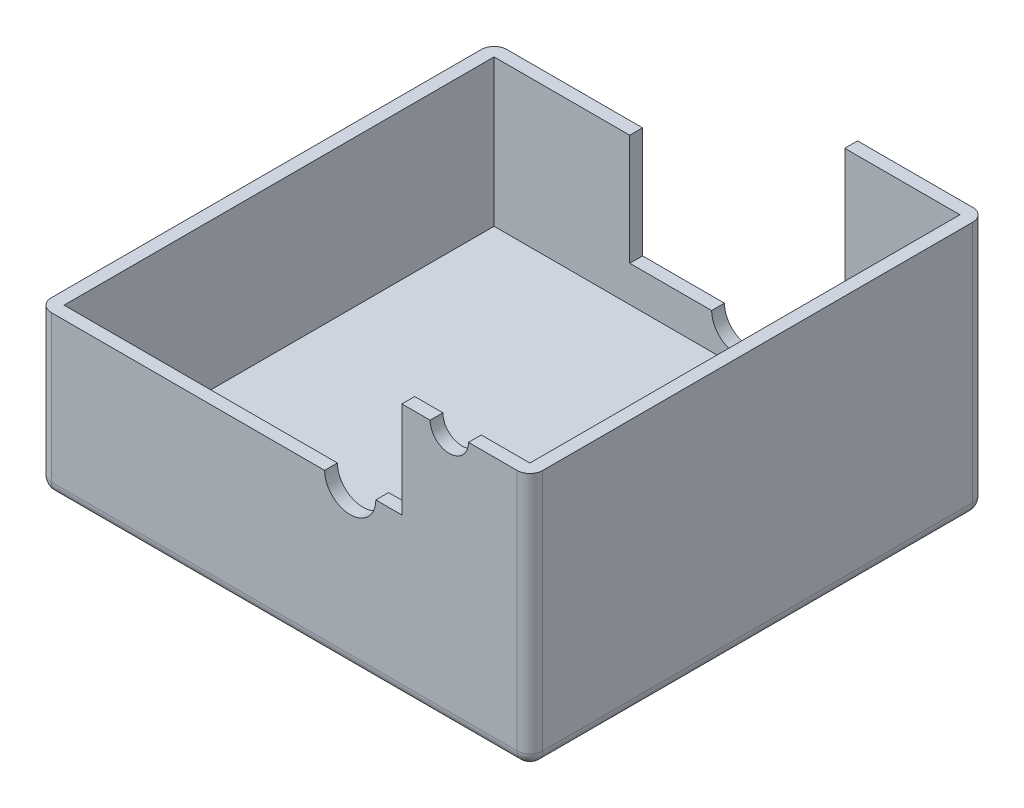
SolidWorks part; units mm, degrees
ref_plane "Front" through (0, 0, 0) normal (0, 0, 1) x (1, 0, 0)
ref_plane "Top" through (0, 0, 0) normal (0, 1, 0) x (1, 0, 0)
ref_plane "Right" through (0, 0, 0) normal (1, 0, 0) x (0, 0, -1)
sketch "Sketch1" plane through (0, 0, 0) normal (0, 1, 0) x (1, 0, 0)
  line L1 (0, 0) -> (96, 0)
  line L2 (0, 0) -> (0, -89)
  line L3 (0, -89) -> (96, -89)
  line L4 (96, 0) -> (96, -89)
  dimension "D1" = 96
  dimension "D2" = 89
extrude "Boss-Extrude1" add sketch "Sketch1" along normal blind 72.5
sketch "Sketch3" plane through (0, 72.5, 0) normal (0, 1, 0) x (1, 0, 0)
  line L8 (2.5, -2.5) -> (2.5, -86.5)
  line L9 (2.5, -86.5) -> (93.5, -86.5)
  line L10 (93.5, -86.5) -> (93.5, -2.5)
  line L11 (93.5, -2.5) -> (2.5, -2.5)
  line L12 (2.5, -2.5) -> (2.5, -86.5)
  line L13 (2.5, -86.5) -> (93.5, -86.5)
  line L14 (93.5, -86.5) -> (93.5, -2.5)
  line L15 (93.5, -2.5) -> (2.5, -2.5)
  dimension "D1" = 2.5
extrude "Cut-Extrude1" cut sketch "Sketch3" against normal blind 70 contours L12 L13 L14 L15
sketch "Sketch5" plane through (0, 0, 89) normal (0, 0, 1) x (1, 0, 0)
  line L0 (0, 0) -> (96, 0) construction
  line L2 (96, 72.5) -> (96, 0) construction
  line L3 (0, 72.5) -> (96, 72.5) construction
  line L4 (0, 72.5) -> (0, 0) construction
  line L5 (0, 31.16) -> (0, 72.5)
  line L6 (0, 72.5) -> (96, 72.5)
  line L7 (96, 72.5) -> (96, 49.95)
  line L8 (96, 49.95) -> (80.25, 49.95)
  line L9 (80.25, 49.95) -> (71, 49.95)
  line L10 (71, 49.95) -> (71, 31.16)
  line L11 (71, 31.16) -> (0, 31.16)
  dimension "D1" = 31.16
  dimension "D2" = 15.75
  dimension "D5" = 22.55
  dimension "D7" = 25
extrude "Cut-Extrude5" cut sketch "Sketch5" against normal through all
sketch "Sketch7" plane through (0, 0, 89) normal (0, 0, 1) x (1, 0, 0)
  line L0 (71, 49.95) -> (96, 49.95) construction
  line L1 (0, 31.16) -> (71, 31.16) construction
  line L2 (96, 49.95) -> (96, 0) construction
  circle A0 centre (80.25, 49.95) radius 3.75
  circle A1 centre (60.9, 31.16) radius 5
  dimension "D1" = 10
  dimension "D2" = 7.5
  dimension "D3" = 15.75
  dimension "D4" = 35.1
extrude "Cut-Extrude6" cut sketch "Sketch7" against normal blind 2.5
sketch "Sketch8" plane through (0, 0, 0) normal (0, 0, -1) x (-1, 0, 0)
  line L2 (-71, 31.16) -> (-71, 9.5)
  line L3 (-71, 9.5) -> (-29, 9.5)
  line L4 (-29, 9.5) -> (-29, 31.16)
  line L5 (0, 31.16) -> (-71, 31.16) construction
  line L6 (-29, 31.16) -> (-71, 31.16)
  line L7 (-96, 0) -> (0, 0) construction
  dimension "D2" = 42
  dimension "D1" = 9.5
extrude "Cut-Extrude7" cut sketch "Sketch8" against normal blind 2.5
sketch "Sketch9" plane through (0, 0, 0) normal (0, 0, -1) x (-1, 0, 0)
  line L0 (-71, 9.5) -> (-29, 9.5) construction
  line L1 (-96, 49.95) -> (-96, 0) construction
  line L2 (-55, 9.5) -> (-45, 9.5)
  arc A0 (-55, 9.5) -> (-45, 9.5) centre (-50, 9.5) ccw
  dimension "D1" = 5
  dimension "D2" = 46
extrude "Cut-Extrude8" cut sketch "Sketch9" against normal blind 2.5
fillet "Fillet1" radius 2.5 8 edges at (0, 15.58, 89) (48, 0, 89) (96, 24.975, 89) (96, 0, 44.5) (96, 24.975, 0) (0, 0, 44.5) (48, 0, 0) (0, 15.58, 0)
